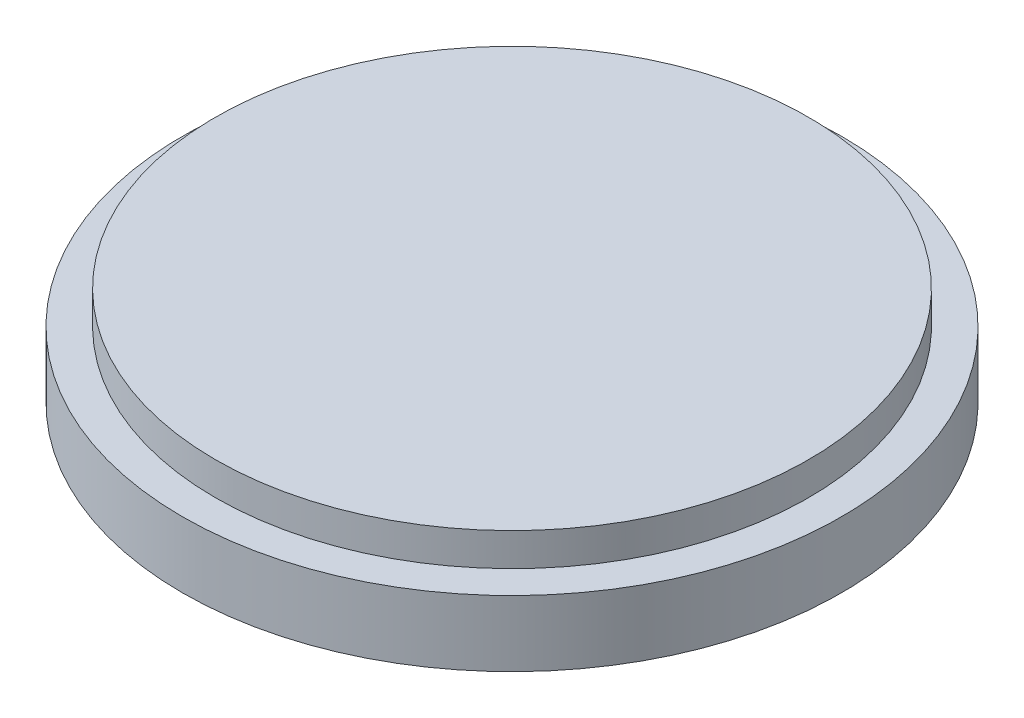
SolidWorks part; units mm, degrees
ref_plane "Alzado" through (0, 0, 0) normal (0, 0, 1) x (1, 0, 0)
ref_plane "Planta" through (0, 0, 0) normal (0, 1, 0) x (1, 0, 0)
ref_plane "Vista lateral" through (0, 0, 0) normal (1, 0, 0) x (0, 0, -1)
sketch "Croquis1" plane through (0, 0, 0) normal (0, 1, 0) x (1, 0, 0)
  circle A0 centre (0, 0) radius 25
  dimension "D1" = 50
extrude "Saliente-Extruir1" add sketch "Croquis1" along normal blind 5
sketch "Croquis2" plane through (0, 5, 0) normal (0, 1, 0) x (1, 0, 0)
  circle A0 centre (0, 0) radius 22.5
  dimension "D1" = 45
extrude "Saliente-Extruir2" add sketch "Croquis2" along normal blind 2.5
